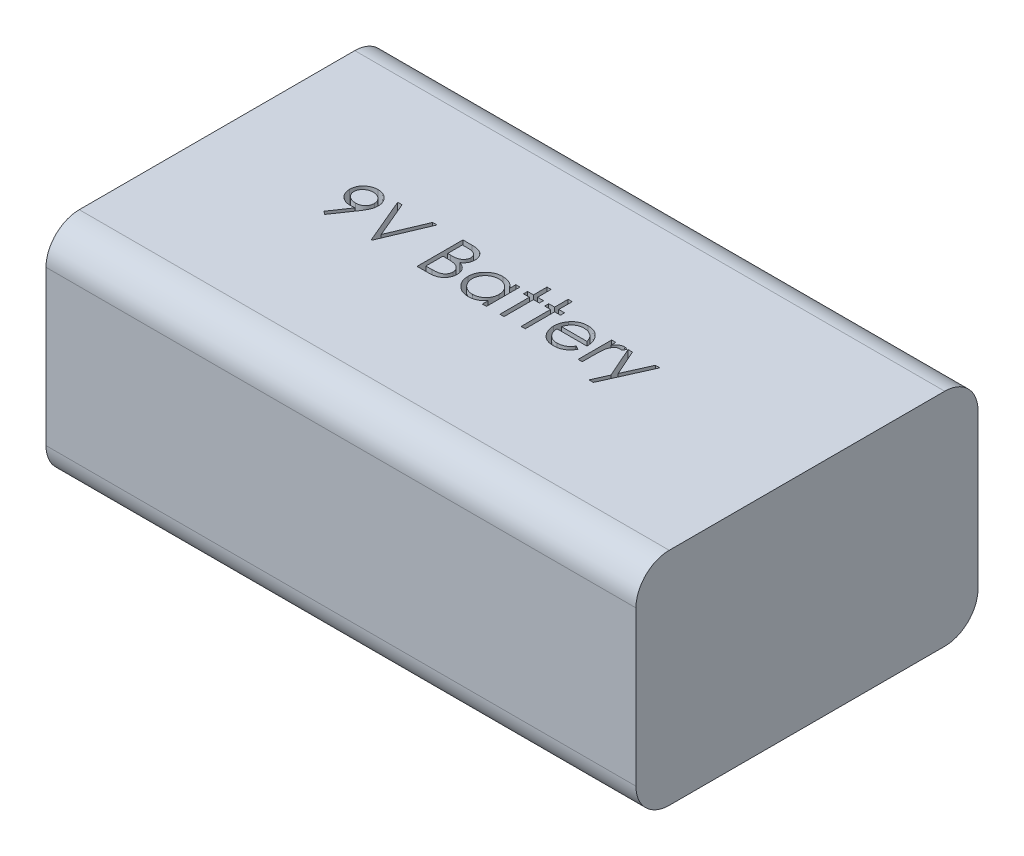
SolidWorks part; units mm, degrees
ref_plane "Front Plane" through (0, 0, 0) normal (0, 0, 1) x (1, 0, 0)
ref_plane "Top Plane" through (0, 0, 0) normal (0, 1, 0) x (1, 0, 0)
ref_plane "Right Plane" through (0, 0, 0) normal (1, 0, 0) x (0, 0, -1)
sketch "Sketch1" plane through (0, 0, 0) normal (0, 1, 0) x (1, 0, 0)
  line L1 (0, 0) -> (47.5742, 0)
  line L2 (0, 0) -> (0, 26.1112)
  line L3 (0, 26.1112) -> (47.5742, 26.1112)
  line L4 (47.5742, 0) -> (47.5742, 26.1112)
  dimension "D1" = 47.5742
  dimension "D2" = 26.1112
extrude "Boss-Extrude1" add sketch "Sketch1" along normal blind 16.8656
sketch "Sketch2" plane through (0, 16.8656, 0) normal (0, 1, 0) x (1, 0, 0)
  text T0 "9V Battery"
extrude "Cut-Extrude1" cut sketch "Sketch2" against normal blind 1.778
sketch "Sketch3" plane through (0, 0, 0) normal (-1, 0, 0) x (0, 0, 1)
  line L3 (-26.1112, 16.8656) -> (0, 16.8656)
  line L5 (-26.1112, 16.8656) -> (-26.1112, 0)
  line L6 (-26.1112, 0) -> (0, 0)
  line L7 (0, 16.8656) -> (0, 0)
  circle A0 centre (-19.5834, 8.4328) radius 3.81
  circle A1 centre (-6.5278, 8.4328) radius 3.81
  dimension "D1" = 7.62
  dimension "D2" = 7.62
extrude "Cut-Extrude2" cut sketch "Sketch3" against normal blind 2.54
fillet "Fillet2" radius 2.54 4 edges at (25.0571, 0, -26.1112) (25.0571, 0, 0) (25.0571, 16.8656, 0) (25.0571, 16.8656, -26.1112)
